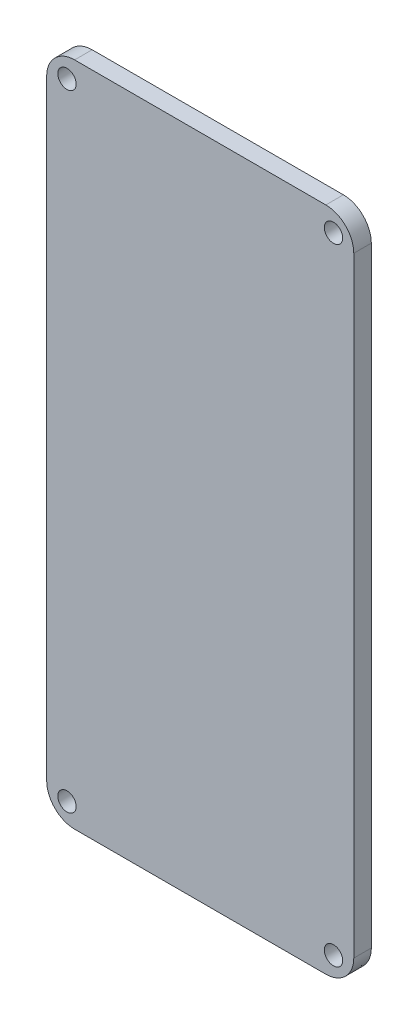
SolidWorks part; units mm, degrees
ref_plane "Alzado" through (0, 0, 0) normal (0, 0, 1) x (1, 0, 0)
ref_plane "Planta" through (0, 0, 0) normal (0, 1, 0) x (1, 0, 0)
ref_plane "Vista lateral" through (0, 0, 0) normal (1, 0, 0) x (0, 0, -1)
sketch "Model" plane through (0, 0, 0) normal (0, 0, 1) x (1, 0, 0)
  line L0 (-30.4205, 55.7989) -> (12.5663, 55.7989)
  line L1 (17.3424, 51.0227) -> (17.3424, -53.425)
  line L2 (12.5663, -58.2012) -> (-30.4205, -58.2012)
  line L3 (-35.1968, -53.425) -> (-35.1968, 51.0227)
  ellipse E0 centre (-31.7272, 52.3291) end of major axis (-31.7272, 53.9003) minor radius 1.5712
  ellipse E1 centre (13.8728, 52.3291) end of major axis (13.8728, 53.9003) minor radius 1.5712
  ellipse E2 centre (-31.7272, -54.7318) end of major axis (-31.7272, -53.1606) minor radius 1.5712
  ellipse E3 centre (13.8728, -54.7318) end of major axis (13.8728, -53.1606) minor radius 1.5712
  spline S0 degree 3 poles (12.5663, 55.7989) (15.1931, 55.7989) (17.3424, 53.6496) (17.3424, 51.0227) knots 0.111111 0.111111 0.111111 0.111111 0.222222 0.222222 0.222222 0.222222
  spline S1 degree 3 poles (17.3424, -53.425) (17.3424, -56.052) (15.1931, -58.2012) (12.5663, -58.2012) knots 0.333333 0.333333 0.333333 0.333333 0.444444 0.444444 0.444444 0.444444
  spline S2 degree 3 poles (-30.4205, -58.2012) (-33.0474, -58.2012) (-35.1968, -56.052) (-35.1968, -53.425) knots 0.555556 0.555556 0.555556 0.555556 0.666667 0.666667 0.666667 0.666667
  spline S3 degree 3 poles (-35.1968, 51.0227) (-35.1968, 53.6496) (-33.0474, 55.7989) (-30.4205, 55.7989) knots 0.777778 0.777778 0.777778 0.777778 1 1 1 1
extrude "Saliente-Extruir1" add sketch "Model" along normal blind 3
